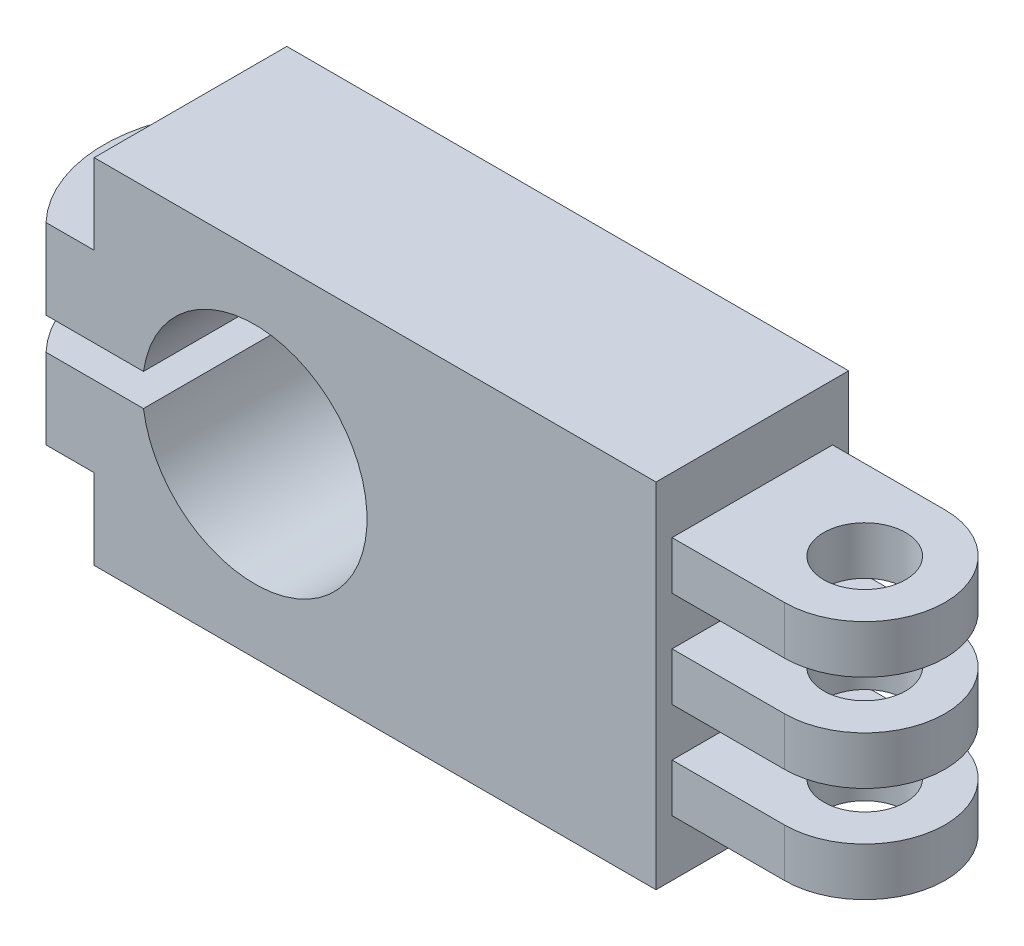
SolidWorks part; units mm, degrees
ref_plane "前视基准面" through (0, 0, 0) normal (0, 0, 1) x (1, 0, 0)
ref_plane "上视基准面" through (0, 0, 0) normal (0, 1, 0) x (1, 0, 0)
ref_plane "右视基准面" through (0, 0, 0) normal (1, 0, 0) x (0, 0, -1)
sketch "草图1" plane through (0, 0, 0) normal (0, 0, 1) x (1, 0, 0)
  line L0 (0, 0) -> (35, 0)
  line L1 (35, 0) -> (35, -3.5)
  line L2 (35, -3.5) -> (47, -3.5)
  line L3 (47, -3.5) -> (47, -6.5)
  line L4 (47, -6.5) -> (35, -6.5)
  line L5 (35, -6.5) -> (35, -9.5)
  line L6 (35, -9.5) -> (47, -9.5)
  line L7 (47, -9.5) -> (47, -12.5)
  line L8 (47, -12.5) -> (35, -12.5)
  line L9 (35, -12.5) -> (35, -15.5)
  line L10 (35, -15.5) -> (47, -15.5)
  line L11 (47, -15.5) -> (47, -18.5)
  line L12 (47, -18.5) -> (35, -18.5)
  line L13 (35, -18.5) -> (35, -22)
  line L14 (35, -22) -> (0, -22)
  line L15 (0, -22) -> (0, -17)
  line L16 (0, -17) -> (-10, -17)
  line L17 (-10, -17) -> (-10, -12)
  line L21 (-10, -10) -> (0, -10)
  line L22 (-10, -10) -> (-10, -5)
  line L26 (0, -10) -> (0, -12)
  line L27 (0, -12) -> (-10, -12)
  line L28 (-10, -5) -> (0, -5)
  line L29 (0, -5) -> (0, 0)
extrude "凸台-拉伸1" add sketch "草图1" along normal blind 12 contours L29 L0 L1 L2 L3 L4 L5 L6 L7 L8 L9 L10 L11 L12 L13 L14 L15 L16 L17 L27 L26 L21 L22 L28
sketch "草图2" plane through (0, -3.5, 0) normal (0, 1, 0) x (1, 0, 0)
  line L0 (47, -6) -> (42, -6) construction
  line L1 (47, -12) -> (47, 0) construction
  circle A0 centre (42, -6) radius 2.55
extrude "切除-拉伸1" cut sketch "草图2" against normal blind 19
sketch "草图3" plane through (0, -3.5, 0) normal (0, 1, 0) x (1, 0, 0)
  line L0 (42, -1) -> (35, -1)
  line L1 (35, -12) -> (35, 0) construction
  line L2 (35, -1) -> (35, 1.3629)
  line L3 (35, 1.3629) -> (53.3289, 1.3629)
  line L4 (53.3289, 1.3629) -> (53.3289, -14.8132)
  line L5 (53.3289, -14.8132) -> (35, -14.8132)
  line L6 (35, -14.8132) -> (35, -11)
  line L7 (35, -11) -> (42, -11)
  arc A0 (42, -11) -> (42, -1) centre (42, -6) ccw
  point P5 (0, 0)
extrude "切除-拉伸2" cut sketch "草图3" against normal blind 19
sketch "草图4" plane through (0, -17, 0) normal (0, -1, 0) x (1, 0, 0)
  line L0 (-10, 6) -> (-2.5, 6) construction
  line L1 (-10, 12) -> (-10, 0) construction
  circle A0 centre (-2.5, 6) radius 1
  point P5 (0, 0)
extrude "切除-拉伸3" cut sketch "草图4" against normal blind 19
sketch "草图5" plane through (0, 0, 12) normal (0, 0, 1) x (1, 0, 0)
  line L0 (0, -11) -> (10, -11) construction
  line L1 (0, -10) -> (0, -12) construction
  line L3 (0, -10) -> (10, -10)
  line L4 (0, -10) -> (0, -12)
  line L5 (0, -12) -> (10, -12)
  line L6 (10, -10) -> (10, -12)
extrude "切除-拉伸4" cut sketch "草图5" against normal blind 19
sketch "草图6" plane through (0, 0, 12) normal (0, 0, 1) x (1, 0, 0)
  line L0 (10, -12) -> (10, -10) construction
  circle A0 centre (10, -11) radius 7
extrude "切除-拉伸5" cut sketch "草图6" against normal blind 19
sketch "草图7" plane through (0, -5, 0) normal (0, 1, 0) x (1, 0, 0)
  line L0 (-10, 0) -> (0, 0) construction
  line L1 (-10, -12) -> (0, -12) construction
  line L2 (-3, -12) -> (-3, -16.2455)
  line L3 (-3, -16.2455) -> (-15.2417, -16.2455)
  line L4 (-15.2417, -16.2455) -> (-15.2417, 3.3262)
  line L5 (-15.2417, 3.3262) -> (-3, 3.3262)
  line L6 (-3, 3.3262) -> (-3, 0)
  arc A0 (-3, 0) -> (-3, -12) centre (3.3167, -6) ccw
extrude "切除-拉伸6" cut sketch "草图7" against normal blind 19
